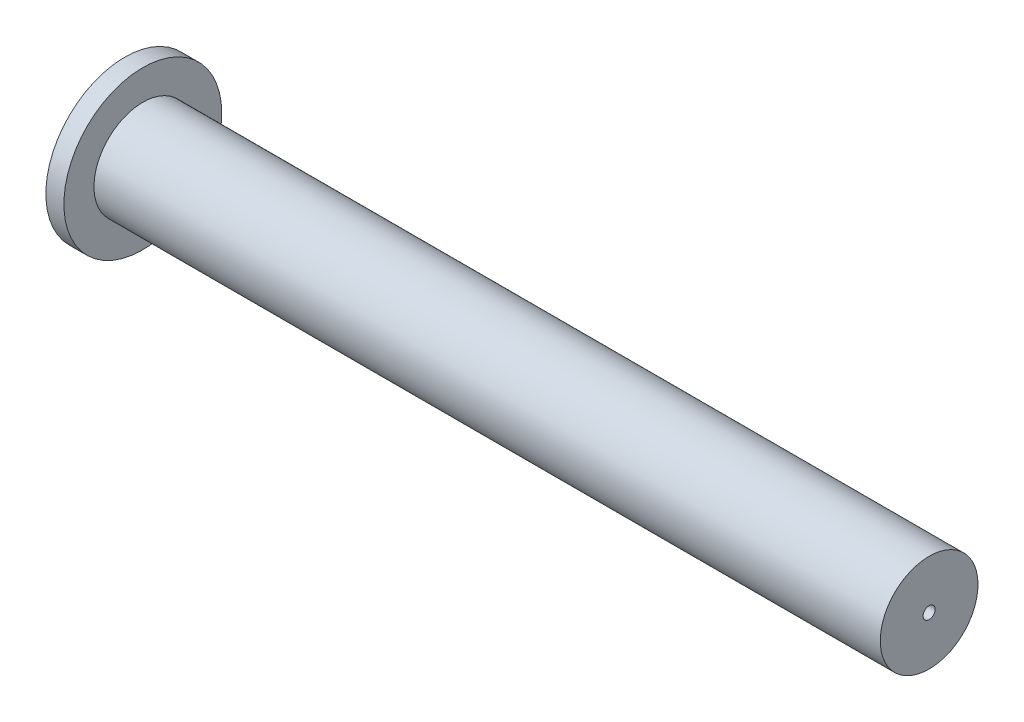
SolidWorks part; units mm, degrees
material "AISI 316 Annealed Stainless Steel Bar (SS)"
ref_plane "Front Plane" through (0, 0, 0) normal (0, 0, 1) x (1, 0, 0)
ref_plane "Top Plane" through (0, 0, 0) normal (0, 1, 0) x (1, 0, 0)
ref_plane "Right Plane" through (0, 0, 0) normal (1, 0, 0) x (0, 0, -1)
sketch "Sketch1" plane through (0, 0, 0) normal (0, 0, 1) x (1, 0, 0)
  line L1 (11, 0.4) -> (11, 3.25)
  line L2 (11, 3.25) -> (-41.3, 3.25)
  line L3 (10, 0.4) -> (11, 0.4)
  line L4 (10, 0.4) -> (10, 2.25)
  line L5 (10, 2.25) -> (-42.5, 2.25)
  line L7 (-42.5, 5.25) -> (-41.3, 5.25)
  line L8 (-41.3, 5.25) -> (-41.3, 3.25)
  line L9 (-42.5, 2.25) -> (-42.5, 5.25)
  dimension "D1" = 3.25
  dimension "D2" = 2.85
  dimension "D3" = 1
  dimension "D4" = 1
  dimension "D5" = 3
  dimension "D6" = 10
  dimension "D7" = 1.2
  dimension "D8" = 53.5
ref_axis "Axis1" through (13.5, 0, 0) along (-1, 0, 0)
revolve "Revolve1" add sketch "Sketch1" angle 360 about axis through (13.5, 0, 0) along (-1, 0, 0)
